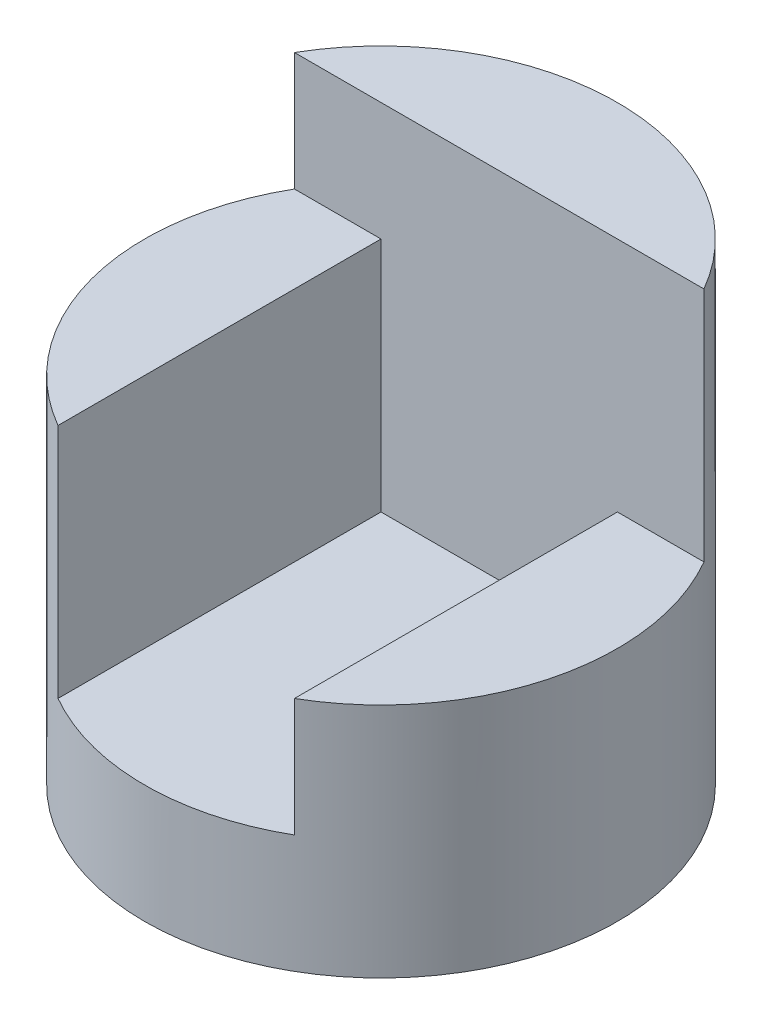
SolidWorks part; units mm, degrees
ref_plane "Front" through (0, 0, 0) normal (0, 0, 1) x (1, 0, 0)
ref_plane "Top" through (0, 0, 0) normal (0, 1, 0) x (1, 0, 0)
ref_plane "Right" through (0, 0, 0) normal (1, 0, 0) x (0, 0, -1)
sketch "Sketch1" plane through (0, 0, 0) normal (0, 1, 0) x (1, 0, 0)
  circle A0 centre (0, 0) radius 2
  dimension "D1" = 4
extrude "Boss-Extrude1" add sketch "Sketch1" along normal blind 4
sketch "Sketch2" plane through (0, 0, 0) normal (0, 0, 1) x (1, 0, 0)
  line L0 (-2, 4) -> (2, 4)
  line L1 (2, 4) -> (2, 3)
  line L2 (2, 0) -> (2, 4) construction
  line L3 (2, 3) -> (1, 3)
  line L4 (1, 3) -> (1, 1)
  line L5 (1, 1) -> (-1, 1)
  line L6 (-1, 1) -> (-1, 3)
  line L7 (-1, 3) -> (-2, 3)
  line L8 (-2, 3) -> (-2, 4)
  dimension "D1" = 1
  dimension "D2" = 1
  dimension "D3" = 1
  dimension "D4" = 1
  dimension "D5" = 2
extrude "Cut-Extrude1" cut sketch "Sketch2" against normal blind 1 and the other way blind 3
sketch "Sketch3" plane through (0, 0, -1) normal (0, 0, 1) x (1, 0, 0)
  line L0 (2, 0) -> (2, 3) construction
  line L1 (1, 3) -> (2, 3)
  line L2 (1, 3) -> (1, 2)
  line L3 (1, 2) -> (2, 2)
  line L4 (2, 3) -> (2, 2)
  dimension "D1" = 1
extrude "Cut-Extrude2" cut sketch "Sketch3" along normal blind 10
